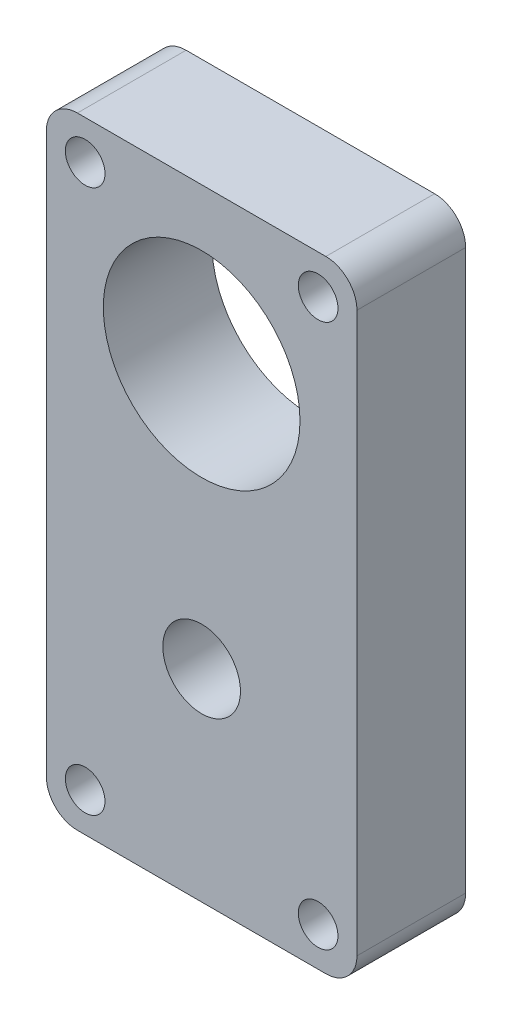
SolidWorks part; units mm, degrees
ref_plane "Front Plane" through (0, 0, 0) normal (0, 0, 1) x (1, 0, 0)
ref_plane "Top Plane" through (0, 0, 0) normal (0, 1, 0) x (1, 0, 0)
ref_plane "Right Plane" through (0, 0, 0) normal (1, 0, 0) x (0, 0, -1)
sketch "Sketch1" plane through (0, 0, 0) normal (0, 0, 1) x (1, 0, 0)
  line L2 (20, -10) -> (20, 20)
  line L3 (20, 20) -> (-20, 20)
  line L4 (-20, -10) -> (-20, 20)
  line L5 (-20, -10) -> (-20, -60)
  line L6 (20, -10) -> (20, -60)
  line L8 (-20, -60) -> (20, -60)
  line L11 (15, -20) -> (-15, -20) construction
  line L12 (-15, 15) -> (15, 15) construction
  line L13 (-15, 15) -> (-15, -55) construction
  line L14 (-15, -55) -> (15, -55) construction
  line L15 (15, 15) -> (15, -55) construction
  circle A0 centre (0, 0) radius 12.665
  circle A1 centre (-15, 15) radius 2.5546
  circle A2 centre (15, 15) radius 2.5546
  circle A5 centre (15, -15) radius 2.5546 [skipped]
  circle A6 centre (-15, -15) radius 2.5546 [skipped]
  circle A7 centre (-15, -55) radius 2.5546
  circle A8 centre (15, -55) radius 2.5546
  circle A9 centre (0, -34) radius 5
  point P0 (0, 0)
  point P19 (0, 20)
  point P25 (0, 0)
  dimension "D2" = 25.33
  dimension "D5" = 30
  dimension "D6" = 5.1092
  dimension "D9" = 10
  dimension "D1" = 40
  dimension "D3" = 80
  dimension "D4" = 20
  dimension "D7" = 4
  dimension "D8" = 70
  dimension "D10" = 34
extrude "Boss-Extrude1" add sketch "Sketch1" along normal blind 14
fillet "Fillet1" radius 4 4 edges at (-20, 20, 7) (20, 20, 7) (20, -60, 7) (-20, -60, 7)
sketch "Sketch6" plane through (0, 0, 14) normal (0, 0, 1) x (1, 0, 0)
  line L0 (-20, 16) -> (-20, -56) construction
  point P0 (-14.1999, 14.9104)
  point P1 (16, 14.9104)
  point P2 (-16, -9.8296)
  point P3 (16, -9.8299)
  dimension "D1" = 24.7403
  dimension "D2" = 30.1999
  dimension "D3" = 24.74
  dimension "D4" = 4
sketch "Sketch11" plane through (0, 0, 0) normal (0, 0, -1) x (-1, 0, 0)
  circle A0 centre (0, -34) radius 7.5
extrude "Boss-Extrude3" add sketch "Sketch11" against normal blind 2
